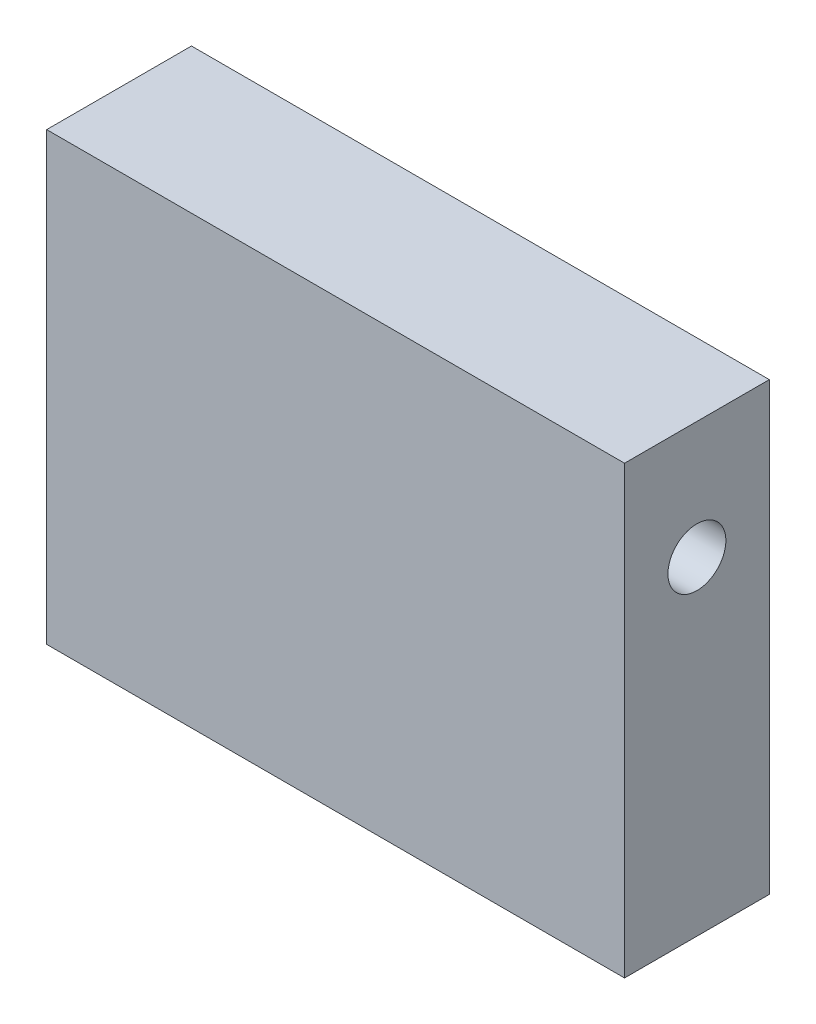
SolidWorks part; units mm, degrees
ref_plane "Front Plane" through (0, 0, 0) normal (0, 0, 1) x (1, 0, 0)
ref_plane "Top Plane" through (0, 0, 0) normal (0, 1, 0) x (1, 0, 0)
ref_plane "Right Plane" through (0, 0, 0) normal (1, 0, 0) x (0, 0, -1)
sketch "Sketch1" plane through (0, 0, 0) normal (0, 0, 1) x (1, 0, 0)
  line L1 (-98.7605, -50.4425) -> (-18.9439, -50.4425)
  line L2 (-98.7605, -50.4425) -> (-98.7605, 11.1382)
  line L3 (-98.7605, 11.1382) -> (-18.9439, 11.1382)
  line L4 (-18.9439, -50.4425) -> (-18.9439, 11.1382)
  line L5 (-98.7605, -50.4425) -> (-18.9439, 11.1382) construction
  line L6 (-98.7605, 11.1382) -> (-18.9439, -50.4425) construction
extrude "Boss-Extrude1" add sketch "Sketch1" along normal blind 20
sketch "Sketch2" plane through (0, 0, 20) normal (0, 0, 1) x (1, 0, 0)
  circle A0 centre (-58.3267, -3.2092) radius 7.2627
sketch "Sketch3" plane through (0, 0, 0) normal (1, 0, 0) x (0, 0, -1)
  line L0 (-10, -5.1016) -> (-10, 11.1382) construction
  line L1 (-20, 11.1382) -> (0, 11.1382) construction
  circle A0 centre (-10, -5.1016) radius 4
  dimension "D1" = 8
extrude "Cut-Extrude1" cut sketch "Sketch3" against normal through all from surface at -18.9439 starting at face at (-18.9439, -19.6522, 10)
